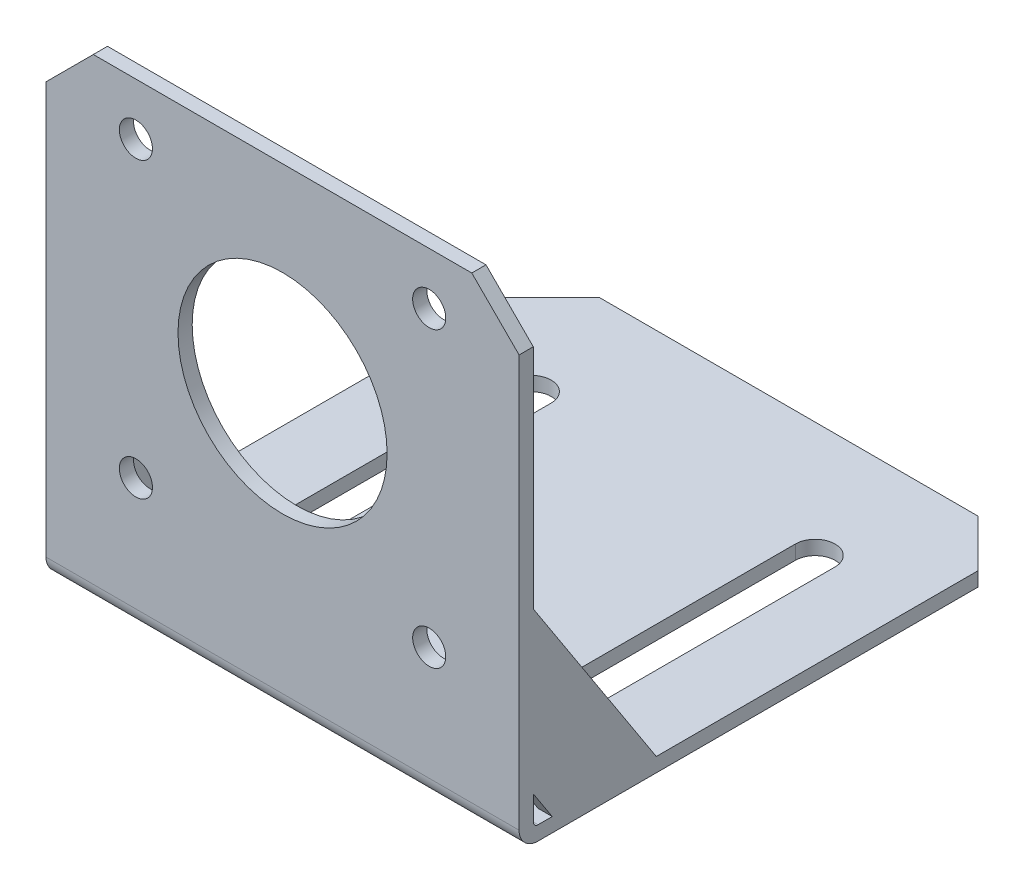
SolidWorks part; units mm, degrees
ref_plane "Ebene vorne" through (0, 0, 0) normal (0, 0, 1) x (1, 0, 0)
ref_plane "Ebene oben" through (0, 0, 0) normal (0, 1, 0) x (1, 0, 0)
ref_plane "Ebene rechts" through (0, 0, 0) normal (1, 0, 0) x (0, 0, -1)
sketch "Skizze1" plane through (0, 0, 0) normal (1, 0, 0) x (0, 0, -1)
  line L0 (0, 2) -> (0, 50.5)
  line L1 (2, 0) -> (53.5, 0)
  arc A0 (0, 2) -> (2, 0) centre (2, 2) ccw
  point P6 (0, 0)
  dimension "D3" = 2
  dimension "D1" = 50.5
  dimension "D2" = 53.5
extrude "Linear-Austragen-Dünn1" add sketch "Skizze1" along normal blind 50 thin
sketch "Skizze2" plane through (0, 0, -1.5) normal (0, 0, -1) x (-1, 0, 0)
  line L0 (-25, 29.5) -> (-25, 50.5) construction
  line L3 (-50, 50.5) -> (0, 50.5) construction
  line L4 (-9.5, 45) -> (-40.5, 45) construction
  line L5 (-9.5, 45) -> (-9.5, 14) construction
  line L6 (-9.5, 14) -> (-40.5, 14) construction
  line L7 (-40.5, 45) -> (-40.5, 14) construction
  line L8 (-9.5, 45) -> (-40.5, 14) construction
  line L9 (-9.5, 14) -> (-40.5, 45) construction
  circle A0 centre (-25, 29.5) radius 11.05
  circle A1 centre (-40.5, 45) radius 1.75
  circle A2 centre (-9.5, 45) radius 1.75
  circle A3 centre (-9.5, 14) radius 1.75
  circle A4 centre (-40.5, 14) radius 1.75
  point P22 (-25, 29.5)
  dimension "D1" = 22.1
  dimension "D3" = 3.5
  dimension "D2" = 31
  dimension "D5" = 21
  dimension "D4" = 4
extrude "Schnitt-Linear austragen1" cut sketch "Skizze2" against normal through all
sketch "Skizze3" plane through (50, 0, 0) normal (1, 0, 0) x (0, 0, -1)
  line L0 (1.5, 21.5) -> (14.5, 1.5)
  line L1 (1.5, 50.5) -> (1.5, 2) construction
  line L2 (2, 1.5) -> (53.5, 1.5) construction
  line L3 (1.5, 4.5769) -> (3.5, 1.5)
  line L4 (1.5, 21.5) -> (1.5, 4.5769)
  line L5 (3.5, 1.5) -> (14.5, 1.5)
  dimension "D1" = 13
  dimension "D2" = 20
  dimension "D3" = 2
extrude "Aufsatz-Linear austragen1" add sketch "Skizze3" against normal blind 1.5
ref_plane "Ebene1" through (25, 0, 0) normal (1, 0, 0) x (0, 0, -1)
mirror "Spiegeln1" about plane through (25, 0, 0) normal (1, 0, 0) of "Aufsatz-Linear austragen1"
sketch "Skizze4" plane through (0, 1.5, 0) normal (0, 1, 0) x (1, 0, 0)
  line L0 (10, 13.7067) -> (10, 41.2933) construction
  line L1 (7.9, 13.7067) -> (7.9, 41.2933)
  line L2 (12.1, 13.7067) -> (12.1, 41.2933)
  line L3 (25, 53.5) -> (25, 1.5) construction
  line L4 (50, 53.5) -> (0, 53.5) construction
  line L5 (25, -27.775) -> (25, 27.775) construction
  line L6 (50, 1.5) -> (0, 1.5) construction
  line L7 (40, 13.7067) -> (40, 41.2933) construction
  line L8 (42.1, 13.7067) -> (42.1, 41.2933)
  line L9 (37.9, 13.7067) -> (37.9, 41.2933)
  line L10 (25, 27.5) -> (0, 27.5) construction
  line L11 (0, 14.5) -> (0, 53.5) construction
  arc A0 (7.9, 13.7067) -> (12.1, 13.7067) centre (10, 13.7067) ccw
  arc A1 (12.1, 41.2933) -> (7.9, 41.2933) centre (10, 41.2933) ccw
  arc A2 (42.1, 13.7067) -> (37.9, 13.7067) centre (40, 13.7067) cw
  arc A3 (37.9, 41.2933) -> (42.1, 41.2933) centre (40, 41.2933) cw
  point P2 (10, 27.5)
  point P18 (40, 27.5)
  dimension "D1" = 30
extrude "Schnitt-Linear austragen2" cut sketch "Skizze4" against normal through all
chamfer "Fase1" distance 5 angle 45 4 edges at (50, 50.5, -0.75) (0, 50.5, -0.75) (0, 0.75, -53.5) (50, 0.75, -53.5)
